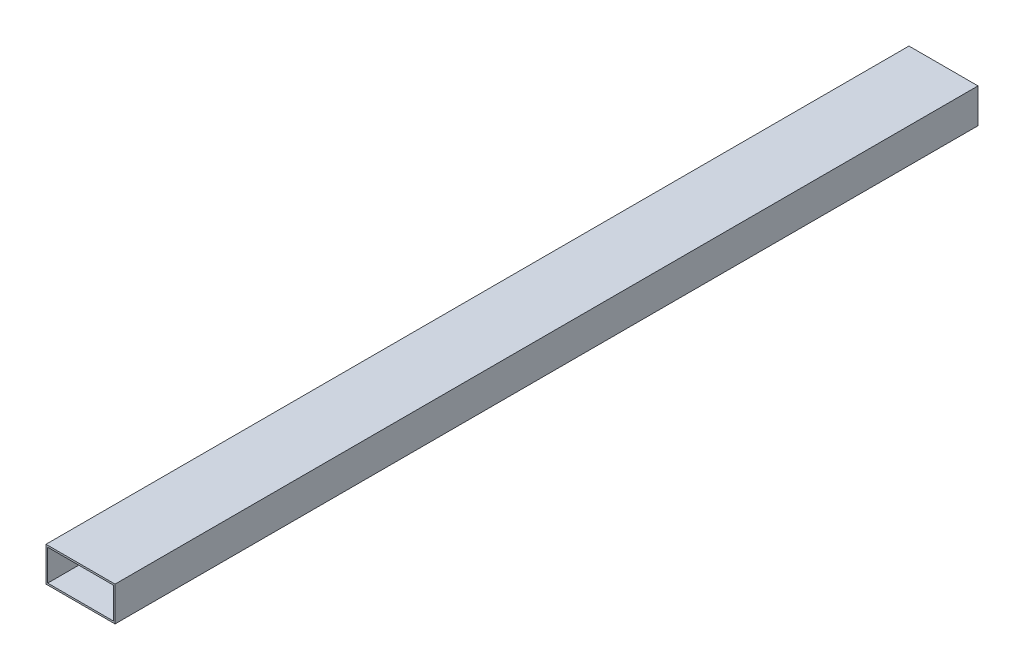
SolidWorks part; units mm, degrees
ref_plane "Front Plane" through (0, 0, 0) normal (0, 0, 1) x (1, 0, 0)
ref_plane "Top Plane" through (0, 0, 0) normal (0, 1, 0) x (1, 0, 0)
ref_plane "Right Plane" through (0, 0, 0) normal (1, 0, 0) x (0, 0, -1)
sketch "Sketch1" plane through (0, 0, 0) normal (0, 0, 1) x (1, 0, 0)
  line L0 (0, 11.5123) -> (0, -11.9084) construction
  line L1 (25.9837, 0) -> (-26.974, 0) construction
  line L2 (-20, 10) -> (20, 10)
  line L3 (20, 10) -> (20, -10)
  line L4 (20, -10) -> (-20, -10)
  line L5 (-20, -10) -> (-20, 10)
  point P7 (0, 10)
  point P10 (20, 0)
  point P11 (-20, 0)
  dimension "D1" = 40
  dimension "D2" = 20
extrude "Boss-Extrude1" add sketch "Sketch1" along normal blind 500
sketch "Sketch2" plane through (0, 0, 500) normal (0, 0, 1) x (1, 0, 0)
  line L8 (-19, 9) -> (-19, -9)
  line L9 (-19, -9) -> (19, -9)
  line L10 (19, -9) -> (19, 9)
  line L11 (19, 9) -> (-19, 9)
  line L12 (-19, 9) -> (-19, -9)
  line L13 (-19, -9) -> (19, -9)
  line L14 (19, -9) -> (19, 9)
  line L15 (19, 9) -> (-19, 9)
  dimension "D1" = 1
extrude "Cut-Extrude1" cut sketch "Sketch2" against normal through all
